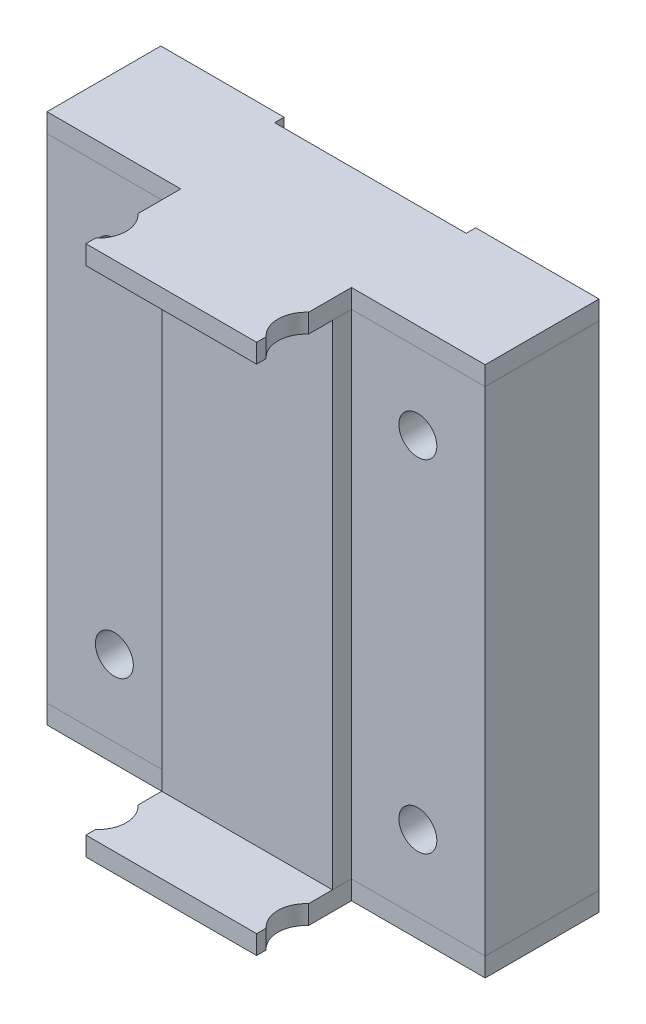
SolidWorks part; units mm, degrees
ref_plane "Front Plane" through (0, 0, 0) normal (0, 0, 1) x (1, 0, 0)
ref_plane "Top Plane" through (0, 0, 0) normal (0, 1, 0) x (1, 0, 0)
ref_plane "Right Plane" through (0, 0, 0) normal (1, 0, 0) x (0, 0, -1)
sketch "Sketch1" plane through (0, 0, 0) normal (0, 1, 0) x (1, 0, 0)
  line L0 (23.1, 0) -> (9, 0)
  line L1 (-23.1, 0) -> (-23.1, 12)
  line L2 (-23.1, 12) -> (-10.1, 12)
  line L3 (-10.1, 12) -> (-10.1, 11)
  line L4 (-10.1, 11) -> (10.1, 11)
  line L5 (0, 11) -> (0, 0) construction
  line L6 (10.1, 12) -> (10.1, 11)
  line L7 (23.1, 12) -> (10.1, 12)
  line L8 (23.1, 0) -> (23.1, 12)
  line L9 (-9, 0) -> (-9, -2)
  line L10 (-9, -2) -> (9, -2)
  line L11 (9, -2) -> (9, 0)
  line L12 (-9, 0) -> (-23.1, 0)
  dimension "D1" = 23.1
  dimension "D2" = 12
  dimension "D3" = 13
  dimension "D4" = 1
  dimension "D5" = 11
  dimension "D6" = 9
  dimension "D7" = 18
  dimension "D8" = 2
  dimension "D9" = 14.1
extrude "Boss-Extrude1" add sketch "Sketch1" along normal mid plane 52
sketch "Sketch2" plane through (0, 0, -12) normal (0, 0, -1) x (-1, 0, 0)
  line L0 (0, -26) -> (0, 26) construction
  line L1 (-10.1, -26) -> (10.1, -26) construction
  line L2 (-10.1, 26) -> (10.1, 26) construction
  line L3 (23.1, 0) -> (-23.1, 0) construction
  line L4 (23.1, 26) -> (23.1, -26) construction
  line L5 (-23.1, 26) -> (-23.1, -26) construction
  circle A0 centre (16, -18) radius 2
  circle A1 centre (-16, -18) radius 2
  circle A2 centre (-16, 18) radius 2
  circle A3 centre (16, 18) radius 2
  dimension "D1" = 4
  dimension "D2" = 16
  dimension "D3" = 18
extrude "Cut-Extrude1" cut sketch "Sketch2" against normal up to next
sketch "Sketch3" plane through (0, 26, 0) normal (0, 1, 0) x (1, 0, 0)
  line L0 (10.1, 11) -> (-10.1, 11)
  line L1 (10.1, 11) -> (-10.1, 11) construction
  line L2 (-10.1, 11) -> (-10.1, 12)
  line L3 (-10.1, 12) -> (-23.1, 12)
  line L4 (-23.1, 12) -> (-23.1, 0)
  line L5 (-23.1, 0) -> (-9, 0)
  line L6 (-9, 0) -> (-9, -4.5139)
  line L7 (-9, -10) -> (9, -10)
  line L9 (0, 0) -> (0, -10) construction
  line L10 (-9, -6.75) -> (-11, -6.75) construction
  line L11 (-9, -8.9861) -> (-9, -10)
  line L13 (9, -8.9861) -> (9, -10)
  line L14 (9, 0) -> (9, -4.5139)
  line L15 (23.1, 0) -> (9, 0)
  line L16 (23.1, 12) -> (23.1, 0)
  line L17 (10.1, 12) -> (23.1, 12)
  line L18 (10.1, 11) -> (10.1, 12)
  arc A0 (-9, -8.9861) -> (-9, -4.5139) centre (-11, -6.75) ccw
  arc A1 (9, -8.9861) -> (9, -4.5139) centre (11, -6.75) cw
  point P32 (0, 11)
  dimension "D2" = 6
  dimension "D1" = 10
  dimension "D3" = 2
  dimension "D4" = 6.5
extrude "Boss-Extrude2" add sketch "Sketch3" along normal blind 2 separate body
mirror "Mirror2" about plane through (0, 0, 0) normal (0, 1, 0) of bodies 103
